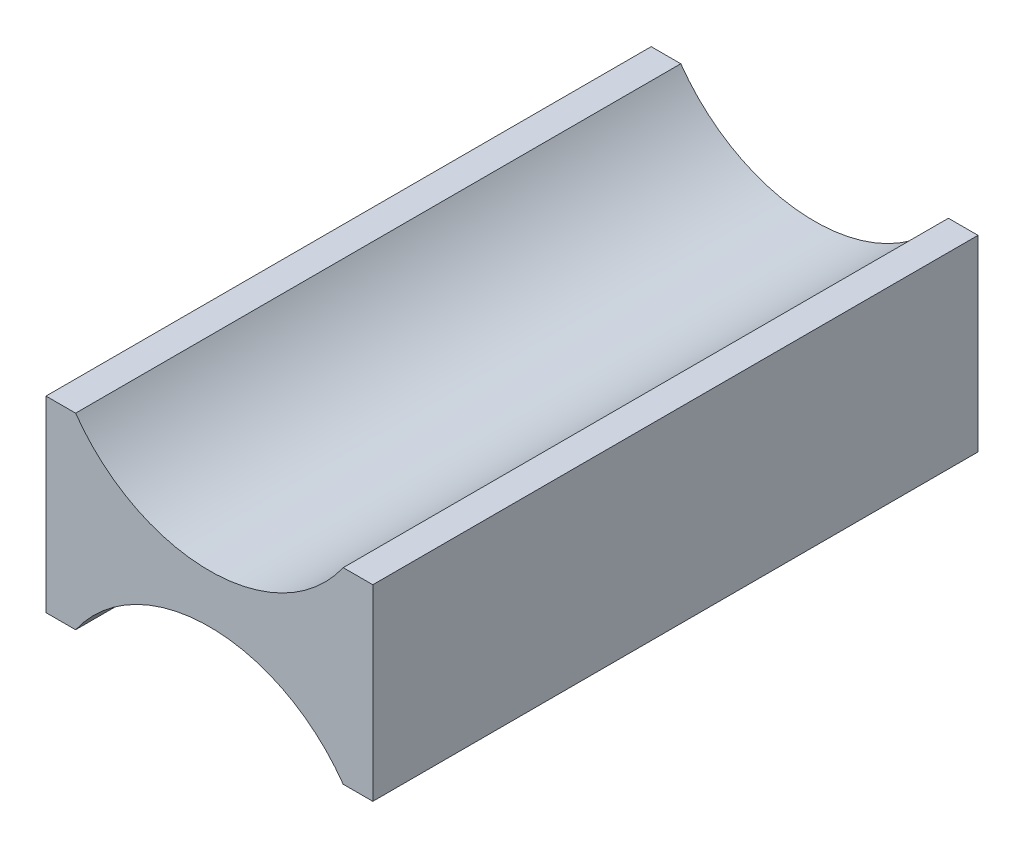
SolidWorks part; units mm, degrees
ref_plane "Plan de face" through (0, 0, 0) normal (0, 0, 1) x (1, 0, 0)
ref_plane "Plan de dessus" through (0, 0, 0) normal (0, 1, 0) x (1, 0, 0)
ref_plane "Plan de droite" through (0, 0, 0) normal (1, 0, 0) x (0, 0, -1)
sketch "Esquisse1" plane through (0, 0, 0) normal (0, 0, 1) x (1, 0, 0)
  line L1 (-2.7, -1.55) -> (2.7, -1.55)
  line L2 (-2.7, -1.55) -> (-2.7, 1.55)
  line L3 (-2.7, 1.55) -> (2.7, 1.55)
  line L4 (2.7, -1.55) -> (2.7, 1.55)
  line L5 (-2.7, -1.55) -> (2.7, 1.55) construction
  line L6 (-2.7, 1.55) -> (2.7, -1.55) construction
  circle A0 centre (0, 3.1) radius 2.7
  circle A1 centre (0, -3.1) radius 2.7
  point P0 (0, 0)
  dimension "D3" = 3.1
  dimension "D5" = 5.4
  dimension "D6" = 5.4
  dimension "D1" = 5.4
  dimension "D2" = 3.1
  dimension "D4" = 3.1
extrude "Boss.-Extru.1" add sketch "Esquisse1" along normal blind 10 contours A1 L1 L4 L3 A0 L2
